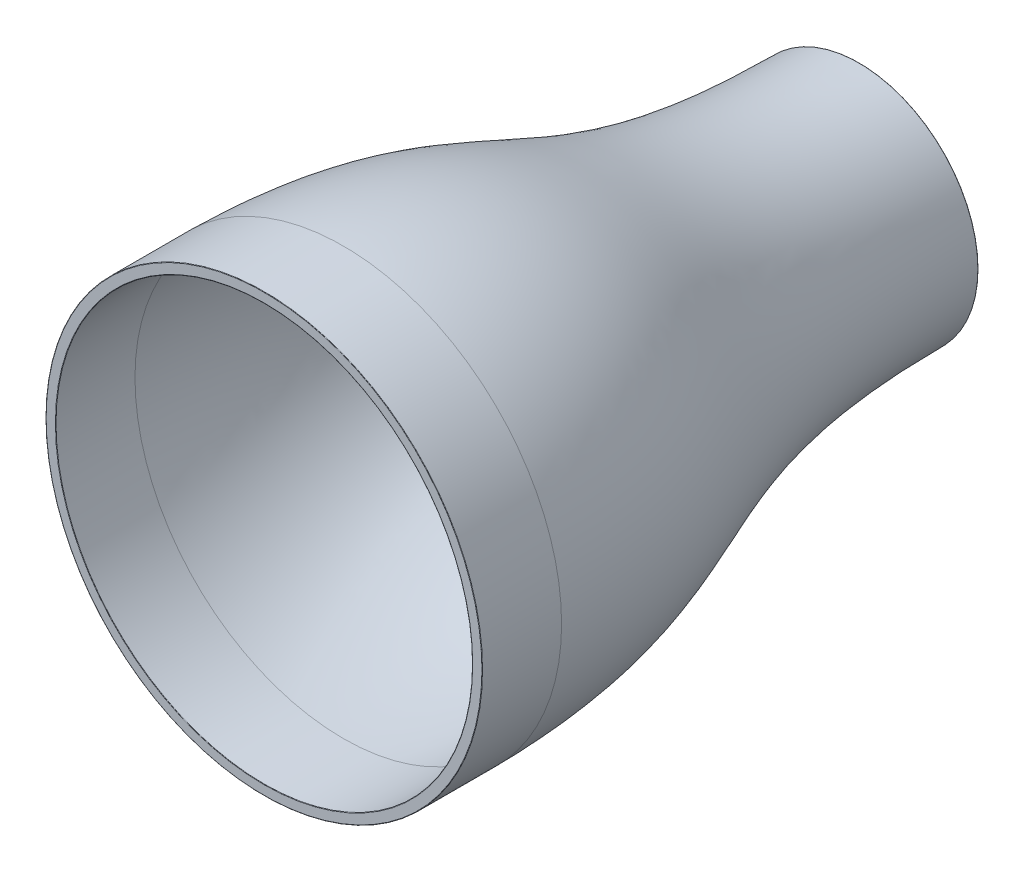
SolidWorks part; units mm, degrees
ref_plane "Front Plane" through (0, 0, 0) normal (0, 0, 1) x (1, 0, 0)
ref_plane "Top Plane" through (0, 0, 0) normal (0, 1, 0) x (1, 0, 0)
ref_plane "Right Plane" through (0, 0, 0) normal (1, 0, 0) x (0, 0, -1)
sketch "Sketch1" plane through (0, 0, 0) normal (1, 0, 0) x (0, 0, -1)
  line L0 (0, 0) -> (300, 0) construction
  line L1 (0, 0) -> (0, 110) construction
  line L2 (0, 110) -> (40, 110)
  line L3 (40, 110) -> (40, 105)
  line L4 (40, 105) -> (0, 105)
  line L5 (0, 105) -> (0, 110)
  line L6 (300, 0) -> (300, 60)
  line L7 (300, 60) -> (270, 60)
  line L8 (270, 60) -> (270, 0)
  line L9 (270, 0) -> (300, 0)
  line L10 (150, 0) -> (150, 90) construction
  spline S0 degree 3 poles (40, 110) (167.8103, 108.0659) (157.7277, 60.1109) (300, 60) knots 0 0 0 0 1 1 1 1
  spline S1 degree 1 poles (39.9243, 105.0006) (299.9961, 55) knots 0 0 1 1 construction
  spline S2 degree 3 poles (39.9243, 105.0006) (40.9047, 104.9857) (42.8773, 104.9501) (46.7253, 104.8573) (51.4223, 104.701) (56.8636, 104.4512) (63.8748, 104.038) (72.1952, 103.3771) (81.5249, 102.3705) (90.2545, 101.1679) (101.1674, 99.3262) (113.586, 96.62) (126.9853, 92.8557) (139.3387, 88.6957) (151.0986, 84.2578) (162.7063, 79.6645) (174.5889, 75.0508) (187.1589, 70.5653) (200.8175, 66.3639) (215.9598, 62.6017) (230.1451, 59.9563) (242.6351, 58.2039) (252.6249, 57.0886) (263.2887, 56.1892) (272.7803, 55.6334) (280.7635, 55.3135) (286.9509, 55.1379) (292.2845, 55.047) (296.6496, 55.0085) (298.885, 55.0009) (299.9961, 55) knots 0 0 0 0 0.007812 0.015625 0.03125 0.046875 0.0625 0.09375 0.125 0.15625 0.1875 0.25 0.3125 0.375 0.4375 0.5 0.5625 0.625 0.6875 0.75 0.8125 0.84375 0.875 0.90625 0.9375 0.953125 0.96875 0.984375 0.992188 1 1 1 1
  dimension "D1" = 30
  dimension "D2" = 40
  dimension "D3" = 60
  dimension "D4" = 30
  dimension "D5" = 60
  dimension "D6" = 300
  dimension "D7" = 110
  dimension "D8" = 5
  dimension "D9" = 150
  dimension "D10" = 90
  dimension "D11" = 5
revolve "Revolve1" add sketch "Sketch1" angle 360 about L0
sketch "Sketch3" plane through (0, 0, -300) normal (0, 0, -1) x (-1, 0, 0)
  circle A0 centre (0, 0) radius 55
  dimension "D1" = 110
extrude "Cut-Extrude1" cut sketch "Sketch3" against normal through all
sketch "Sketch11" plane through (0, 0, 0) normal (0, 0, 1) x (1, 0, 0)
  line L0 (0, 105) -> (0, -105)
  circle A0 centre (0, 0) radius 105 construction
  circle A1 centre (0, 0) radius 105 construction
fillet "Fillet1" radius 0.2 4 edges at (60, 0, -300) (-55, 0, -300) (105, 0, 0) (110, 0, 0)
